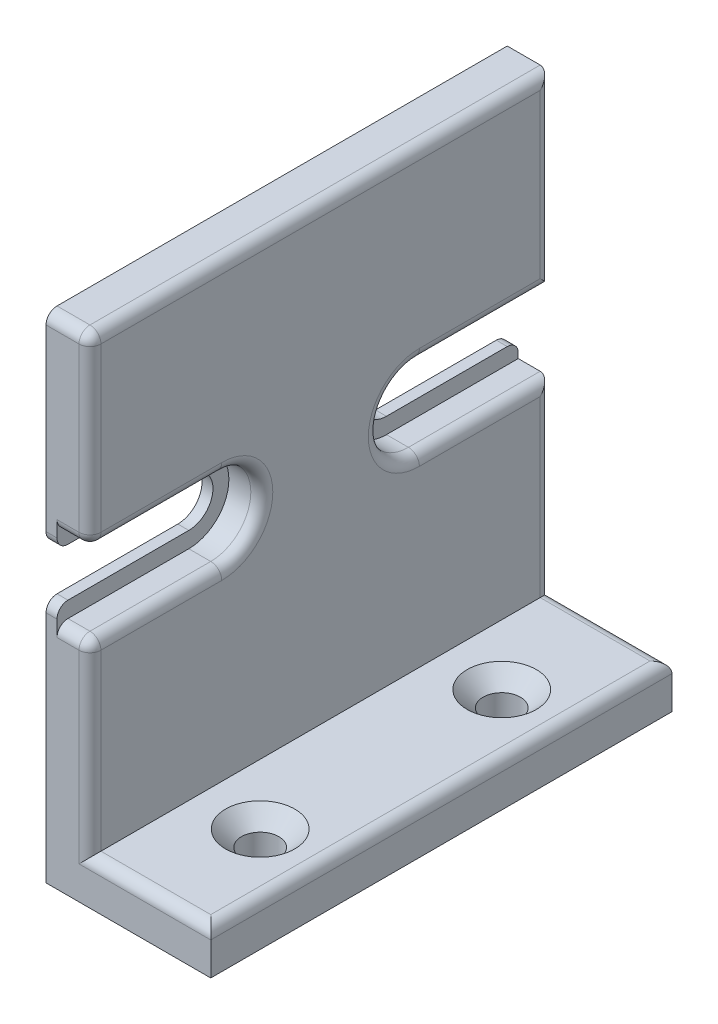
SolidWorks part; units mm, degrees
ref_plane "Спереди" through (0, 0, 0) normal (0, 0, 1) x (1, 0, 0)
ref_plane "Сверху" through (0, 0, 0) normal (0, 1, 0) x (1, 0, 0)
ref_plane "Справа" through (0, 0, 0) normal (1, 0, 0) x (0, 0, -1)
sketch "Sketch1" plane through (0, 0, 0) normal (0, 0, 1) x (1, 0, 0)
  line L0 (-124.3735, 69.4896) -> (-124.3735, 24.4896)
  line L1 (-124.3735, 24.4896) -> (-109.3735, 24.4896)
  line L2 (-109.3735, 24.4896) -> (-109.3735, 28.4896)
  line L3 (-109.3735, 28.4896) -> (-120.3735, 28.4896)
  line L4 (-120.3735, 28.4896) -> (-120.3735, 69.4896)
  line L5 (-120.3735, 69.4896) -> (-124.3735, 69.4896)
  dimension "D1" = 4
  dimension "D2" = 4
  dimension "D3" = 15
  dimension "D4" = 45
extrude "Boss-Extrude1" add sketch "Sketch1" along normal blind 42
sketch "Sketch2" plane through (-120.3735, 0, 0) normal (1, 0, 0) x (0, 0, -1)
  line L0 (-42, 52.6396) -> (-30, 52.6396)
  line L1 (-42, 28.4896) -> (-42, 69.4896) construction
  line L3 (-30, 45.3396) -> (-42, 45.3396)
  line L4 (-42, 45.3396) -> (-42, 52.6396)
  line L5 (-42, 28.4896) -> (0, 28.4896) construction
  line L6 (-21, 69.4896) -> (-21, 28.4896) construction
  line L7 (-42, 69.4896) -> (0, 69.4896) construction
  line L8 (-42, 28.4896) -> (0, 28.4896) construction
  line L9 (0, 48.9896) -> (-43.5, 48.9896) construction
  line L10 (-30, 52.6396) -> (-30, 45.3396) construction
  line L11 (0, 28.4896) -> (0, 69.4896) construction
  arc A0 (-30, 45.3396) -> (-30, 52.6396) centre (-30, 48.9896) ccw
  dimension "D1" = 7.3
  dimension "D2" = 12
  dimension "D3" = 16.85
extrude "Cut-Extrude1" cut sketch "Sketch2" against normal blind 3
sketch "Sketch4" plane through (-123.3735, 0, 0) normal (1, 0, 0) x (0, 0, -1)
  line L0 (-40.2305, 52.6396) -> (-40.2305, 45.3396) construction
  line L1 (-30, 52.6396) -> (-42, 52.6396) construction
  line L2 (-42, 45.3396) -> (-30, 45.3396) construction
  line L4 (-40.2305, 48.9896) -> (-42, 48.9896) construction
  line L5 (-42, 52.6396) -> (-42, 45.3396) construction
  line L9 (-42, 45.3396) -> (-30, 45.3396) construction
  line L10 (-42, 51.1896) -> (-42, 52.6396) construction
  line L11 (-42, 51.1896) -> (-42, 46.7896)
  line L12 (-42, 46.7896) -> (-30, 46.7896)
  line L13 (-42, 51.1896) -> (-30, 51.1896)
  line L14 (-42, 46.7896) -> (-42, 45.3396) construction
  line L15 (-27.8, 48.9896) -> (-26.35, 48.9896) construction
  arc A0 (-30, 45.3396) -> (-30, 52.6396) centre (-30, 48.9896) ccw construction
  arc A2 (-30, 51.1896) -> (-30, 46.7896) centre (-30, 48.9896) cw
  dimension "D2" = 4.4
other "AlignGroup1"
other "AlignGroup2"
extrude "Cut-Extrude2" cut sketch "Sketch4" against normal through all
sketch "Sketch5" plane through (-120.3735, 0, 0) normal (1, 0, 0) x (0, 0, -1)
  line L0 (-21, 69.4896) -> (-21, 28.4896) construction
  line L1 (-42, 69.4896) -> (0, 69.4896) construction
  line L2 (-42, 28.4896) -> (0, 28.4896) construction
  point P6 (0, 0)
ref_plane "Plane1" through (0, 0, 21) normal (0, 0, 1) x (0, -1, 0)
mirror "Mirror2" about plane through (0, 0, 21) normal (0, 0, 1) of "Cut-Extrude2", "Cut-Extrude1"
sketch "Sketch6" plane through (0, 28.4896, 0) normal (0, 1, 0) x (1, 0, 0)
  line L0 (-114.8735, -42) -> (-114.8735, 0) construction
  line L1 (-109.3735, -42) -> (-120.3735, -42) construction
  line L2 (-109.3735, 0) -> (-120.3735, 0) construction
  line L3 (-120.3735, -42) -> (-120.3735, 0) construction
  line L4 (-120.3735, -32) -> (-109.3735, -32) construction
  line L5 (-109.3735, -42) -> (-109.3735, 0) construction
  line L6 (-120.3735, -10) -> (-109.3735, -10) construction
  line L7 (-116.9788, -10) -> (-116.9788, 0) construction
  line L8 (-117.1849, -32) -> (-117.1849, -42) construction
  dimension "D1" = 10
sketch "Sketch7" plane through (0, 28.4896, 0) normal (0, 1, 0) x (1, 0, 0)
  line L0 (-120.3735, -32) -> (-109.3735, -32) construction
  line L1 (-114.8735, -42) -> (-114.8735, 0) construction
  line L2 (-120.3735, -10) -> (-109.3735, -10) construction
  point P4 (-114.8735, -32)
  point P6 (-114.8735, -32)
  point P8 (-114.8735, -10)
  point P9 (0, 0)
hole_wizard "CSK for M3 Flat Head Machine Screw1" positions "Sketch8" profile "Sketch10" countersink size "M3" standard "ANSI Metric" end condition through all
sketch "Sketch8" plane through (0, 28.4896, 0) normal (0, 1, 0) x (1, 0, 0)
  point P0 (-114.8735, -32)
  point P3 (-114.8735, -10)
sketch "Sketch10" plane through (-114.8735, 28.4896, 32) normal (1, 0, 0) x (0, 0, 1)
  line L0 (0, 0) -> (0, 4)
  line L1 (0, 4) -> (1.7, 4)
  line L2 (1.7, 4) -> (1.7, 1.45)
  line L3 (1.7, 1.45) -> (3.15, 0)
  line L5 (3.15, 0) -> (0, 0)
  line L6 (-1.7, 1.45) -> (-3.15, 0) construction
  line L11 (0, -6.35) -> (0, 107.95) construction
  dimension "Thru Hole Dia." = 3.4
  dimension "Thru Hole Depth" = 4
  dimension "Near C'Sink Dia." = 6.3
  dimension "Near C'Sink Angle" = 90
fillet "Fillet3" radius 1 1 edges at (-120.3735, 36.9146, 42)
fillet "Fillet4" radius 1 1 edges at (-120.3735, 61.0646, 42)
fillet "Fillet5" radius 1 7 edges at (-122.3735, 52.6396, 42) (-120.6664, 52.6396, 41.7071) (-120.3735, 52.6396, 35.5) (-120.3735, 48.9896, 26.35) (-120.3735, 45.3396, 35.5) (-122.3735, 45.3396, 42) (-120.6664, 45.3396, 41.7071)
fillet "Fillet6" radius 1 11 edges at (-122.8735, 69.4896, 42) (-120.6664, 69.4896, 41.7071) (-115.3735, 28.4896, 42) (-109.3735, 28.4896, 21) (-114.8735, 28.4896, 0) (-120.3735, 36.9146, 0) (-120.3735, 48.9896, 15.65) (-120.3735, 45.3396, 6) (-120.3735, 52.6396, 6) (-120.3735, 61.0646, 0) (-120.3735, 69.4896, 20.5)
fillet "Fillet7" radius 1 1 edges at (-123.8735, 51.1896, 42)
fillet "Fillet8" radius 1 3 edges at (-123.8735, 46.7896, 42) (-123.8735, 51.1896, 0) (-123.8735, 46.7896, 0)
